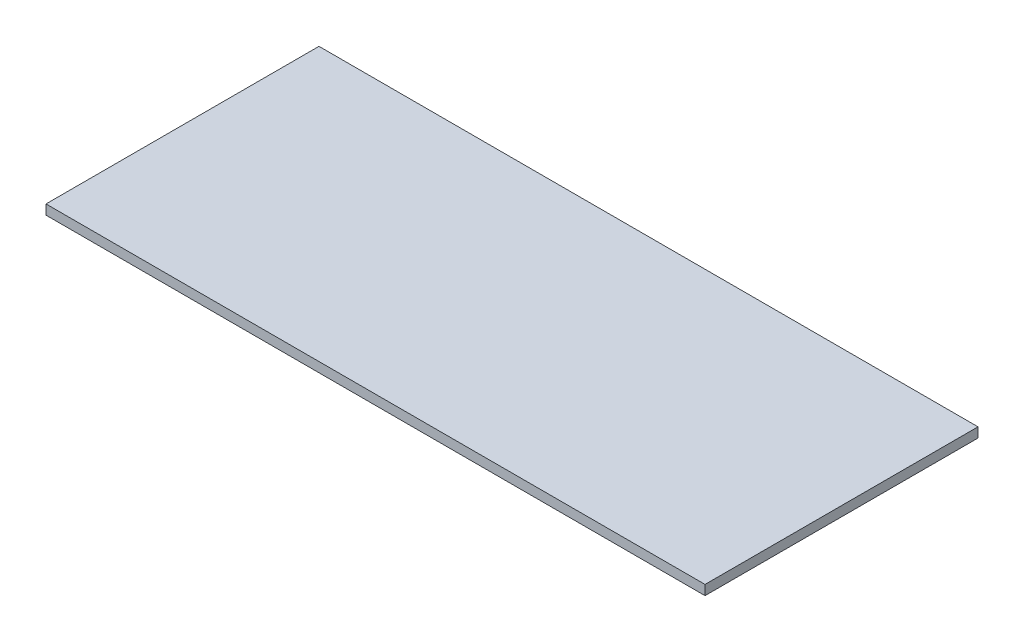
SolidWorks part; units mm, degrees
ref_plane "Front Plane" through (0, 0, 0) normal (0, 0, 1) x (1, 0, 0)
ref_plane "Top Plane" through (0, 0, 0) normal (0, 1, 0) x (1, 0, 0)
ref_plane "Right Plane" through (0, 0, 0) normal (1, 0, 0) x (0, 0, -1)
sketch "Sketch1" plane through (0, 0, 0) normal (0, 1, 0) x (1, 0, 0)
  line L1 (0, 0) -> (429.26, 0)
  line L2 (0, 0) -> (0, 177.8)
  line L3 (0, 177.8) -> (429.26, 177.8)
  line L4 (429.26, 0) -> (429.26, 177.8)
  dimension "D1" = 429.26
  dimension "D2" = 177.8
extrude "Boss-Extrude1" add sketch "Sketch1" along normal blind 6.35
